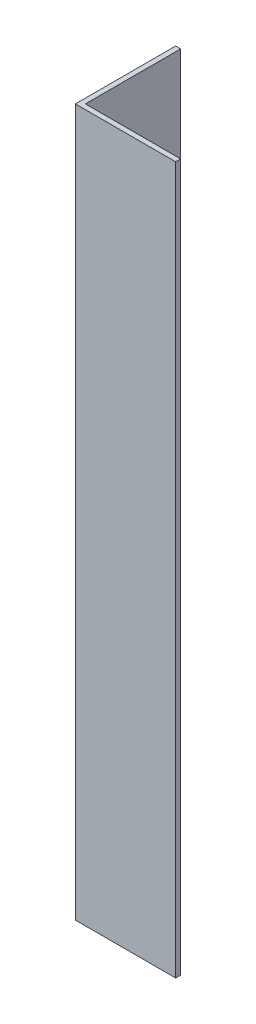
SolidWorks part; units mm, degrees
material "1060 Сплав"
ref_plane "Спереди" through (0, 0, 0) normal (0, 0, 1) x (1, 0, 0)
ref_plane "Сверху" through (0, 0, 0) normal (0, 1, 0) x (1, 0, 0)
ref_plane "Справа" through (0, 0, 0) normal (1, 0, 0) x (0, 0, -1)
sketch "Эскиз1" plane through (0, 0, 0) normal (0, 1, 0) x (1, 0, 0)
  line L0 (0, 0) -> (0, 20)
  line L1 (0, 20) -> (1, 20)
  line L2 (1, 20) -> (1, 1)
  line L3 (1, 1) -> (20, 1)
  line L4 (20, 1) -> (20, 0)
  line L5 (20, 0) -> (0, 0)
  dimension "D1" = 1
  dimension "D2" = 20
extrude "Бобышка-Вытянуть1" add sketch "Эскиз1" along normal blind 141
